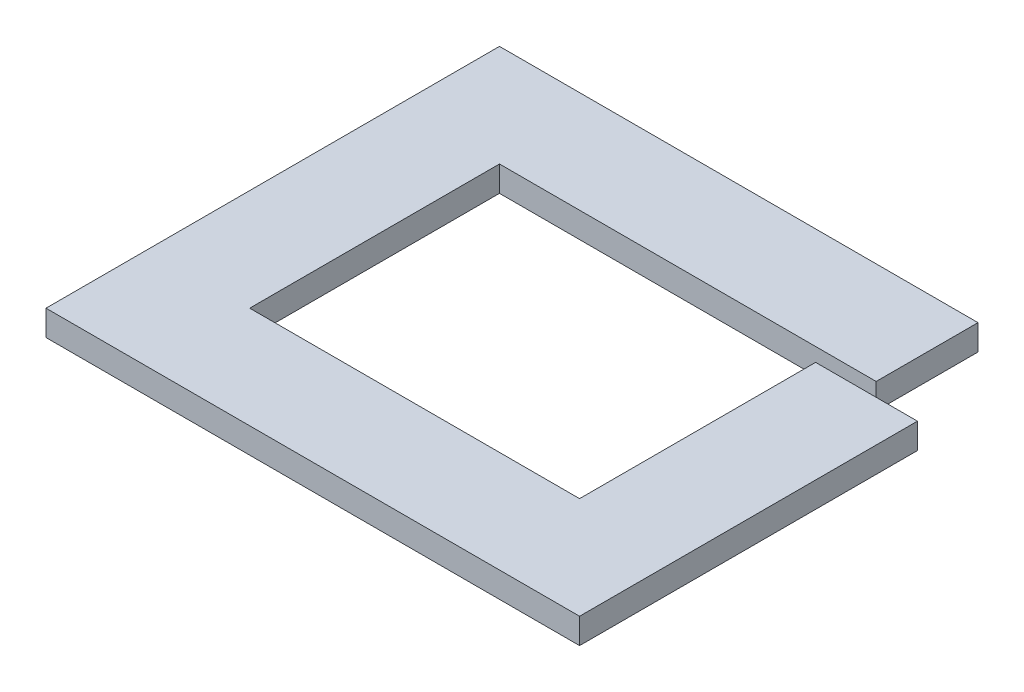
SolidWorks part; units mm, degrees
ref_plane "Front Plane" through (0, 0, 0) normal (0, 0, 1) x (1, 0, 0)
ref_plane "Top Plane" through (0, 0, 0) normal (0, 1, 0) x (1, 0, 0)
ref_plane "Right Plane" through (0, 0, 0) normal (1, 0, 0) x (0, 0, -1)
sketch "Sketch1" plane through (0, 5294.4571, 0) normal (0, 1, 0) x (1, 0, 0)
  line L1 (-23193.7901, -39924.6674) -> (-23113.7901, -39924.6674)
  line L2 (-23193.7901, -39924.6674) -> (-23193.7901, -40200.8713)
  line L3 (-23193.7901, -40200.8713) -> (-23113.7901, -40200.8713)
  line L4 (-23113.7901, -39924.6674) -> (-23113.7901, -40200.8713)
  line L5 (-23193.7901, -40200.8713) -> (-22854.67, -40200.8713)
  line L6 (-23193.7901, -40200.8713) -> (-23193.7901, -40280.8713)
  line L7 (-23193.7901, -40280.8713) -> (-22854.67, -40280.8713)
  line L8 (-22854.67, -40200.8713) -> (-22854.67, -40280.8713)
  line L9 (-23113.7901, -39924.6674) -> (-22817.9109, -39924.6674)
  line L10 (-23113.7901, -39924.6674) -> (-23113.7901, -40004.6674)
  line L11 (-23113.7901, -40004.6674) -> (-22817.9109, -40004.6674)
  line L12 (-22817.9109, -39924.6674) -> (-22817.9109, -40004.6674)
  line L13 (-22854.67, -40280.8713) -> (-22774.67, -40280.8713)
  line L14 (-22854.67, -40280.8713) -> (-22854.67, -40015.4674)
  line L15 (-22854.67, -40015.4674) -> (-22774.67, -40015.4674)
  line L16 (-22774.67, -40280.8713) -> (-22774.67, -40015.4674)
  line L17 (-22817.9109, -39626.9674) -> (-22817.9109, -39781.9674) construction
  line L18 (-22865.6109, -40015.4674) -> (-22763.6109, -40015.4674) construction
  point P14 (0, 0)
  line M11 (-22914.6109, -40028.1674) -> (-22674.6109, -40028.1674)
  line M13 (-22674.6109, -40015.4674) -> (-22914.6109, -40015.4674)
  dimension "D1" = 80
extrude "Boss-Extrude1" add sketch "Sketch1" along normal blind 20 from offset 550 contours L4 L1 L2 L3 | L8 L5 L3 L6 L7 | L13 L16 L14 L8 M11 | L12 L9 L4 L11 | L16 L14 M11 M13
